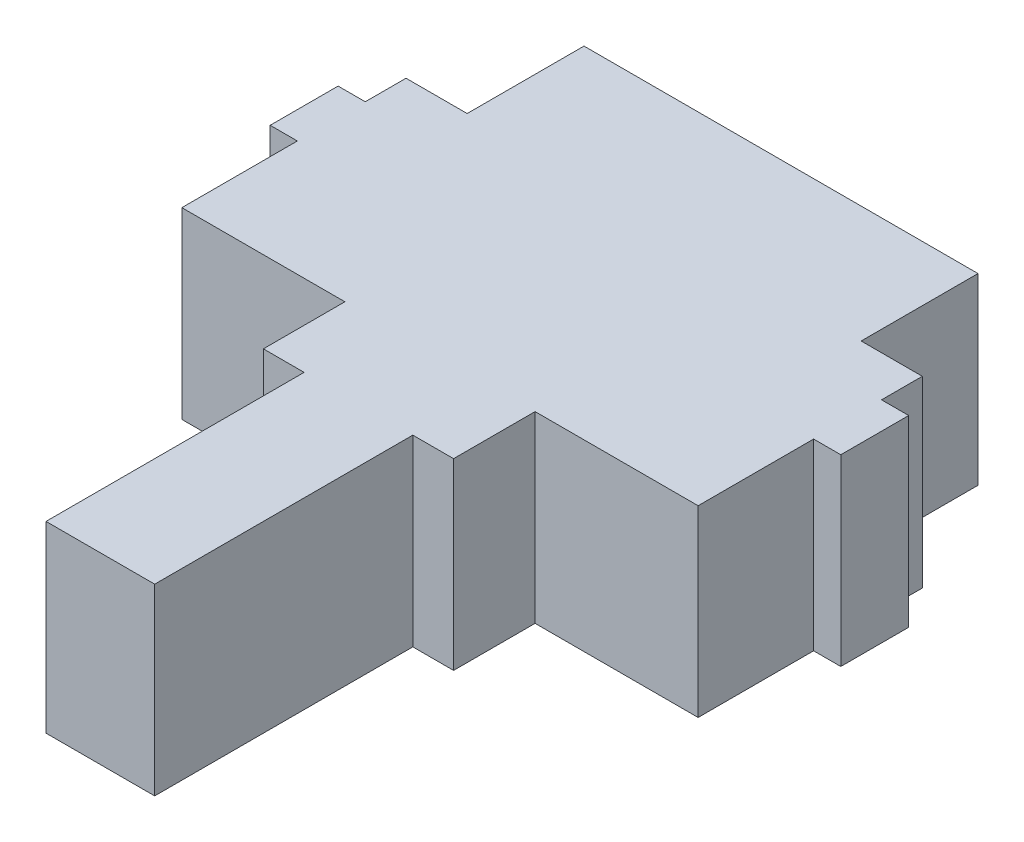
SolidWorks part; units mm, degrees
ref_plane "Front Plane" through (0, 0, 0) normal (0, 0, 1) x (1, 0, 0)
ref_plane "Top Plane" through (0, 0, 0) normal (0, 1, 0) x (1, 0, 0)
ref_plane "Right Plane" through (0, 0, 0) normal (1, 0, 0) x (0, 0, -1)
sketch "Sketch1" plane through (0, 0, 0) normal (0, 1, 0) x (1, 0, 0)
  line L0 (171.7176, 638.5479) -> (904.2727, 651.3347) construction
  line L6 (29.8169, 4.4939) -> (38.0666, 4.4939)
  line L7 (38.0666, 23.4939) -> (38.0666, 4.4939)
  line L8 (38.0666, 23.4939) -> (41.0666, 23.4939)
  line L9 (19.5666, 54.5939) -> (25.0666, 54.5939)
  line L10 (19.5666, 45.9939) -> (19.5666, 54.5939)
  line L11 (41.0666, 23.4939) -> (41.0666, 29.4939)
  line L12 (41.0666, 29.4939) -> (53.0666, 29.4939)
  line L13 (15.0666, 45.9939) -> (19.5666, 45.9939)
  line L14 (15.0666, 42.9939) -> (15.0666, 45.9939)
  line L15 (53.0666, 29.4939) -> (53.0666, 37.9939)
  line L16 (53.0666, 37.9939) -> (55.0666, 37.9939)
  line L17 (13.0666, 37.9939) -> (13.0666, 42.9939)
  line L18 (53.0666, 42.9939) -> (55.0666, 42.9939)
  line L19 (55.0666, 37.9939) -> (55.0666, 42.9939)
  line L20 (15.0666, 42.9939) -> (13.0666, 42.9939)
  line L21 (53.0666, 42.9939) -> (53.0666, 45.9939)
  line L22 (53.0666, 45.9939) -> (48.5666, 45.9939)
  line L23 (15.0666, 37.9939) -> (13.0666, 37.9939)
  line L24 (15.0666, 29.4939) -> (15.0666, 37.9939)
  line L25 (48.5666, 45.9939) -> (48.5666, 54.5939)
  line L26 (48.5666, 54.5939) -> (43.0666, 54.5939)
  line L28 (27.0666, 29.4939) -> (15.0666, 29.4939)
  line L29 (27.0666, 23.4939) -> (27.0666, 29.4939)
  line L31 (30.0666, 23.4939) -> (27.0666, 23.4939)
  line L32 (30.0666, 23.4939) -> (30.0666, 4.4939)
  line L35 (38.3163, 4.4939) -> (30.0666, 4.4939)
  line L36 (25.0666, 54.5939) -> (43.0666, 54.5939)
  point P11 (34.0666, 53.9939)
  dimension "D2" = 3
  dimension "D3" = 12
  dimension "D4" = 2
  dimension "D5" = 4.5
  dimension "D6" = 5.5
  dimension "D7" = 4.4939
  dimension "D8" = 8.6
  dimension "D10" = 5
  dimension "D11" = 8.5
  dimension "D12" = 19
  dimension "D13" = 6
  dimension "D14" = 53.9939
extrude "Boss-Extrude1" add sketch "Sketch1" along normal blind 13.5 contours L36 L9 L10 L13 L14 L20 L17 L23 L24 L28 L29 L31 L32 L6 L7 L8 L11 L12 L15 L16 L19 L18 L21 L22 L25 L26
sketch "Sketch2" plane through (0, 0, 0) normal (0, -1, 0) x (1, 0, 0)
  line L0 (27.0666, -29.4939) -> (27.0666, -33.2041) construction
  line L1 (27.0666, -29.4939) -> (41.0666, -29.4939) construction
  line L2 (41.0666, -29.4939) -> (53.0666, -29.4939) construction
  circle A0 centre (34.0666, -32.9939) radius 2.5
  dimension "D1" = 3.5
extrude "Boss-Extrude2" add sketch "Sketch2" along normal blind 2.5
